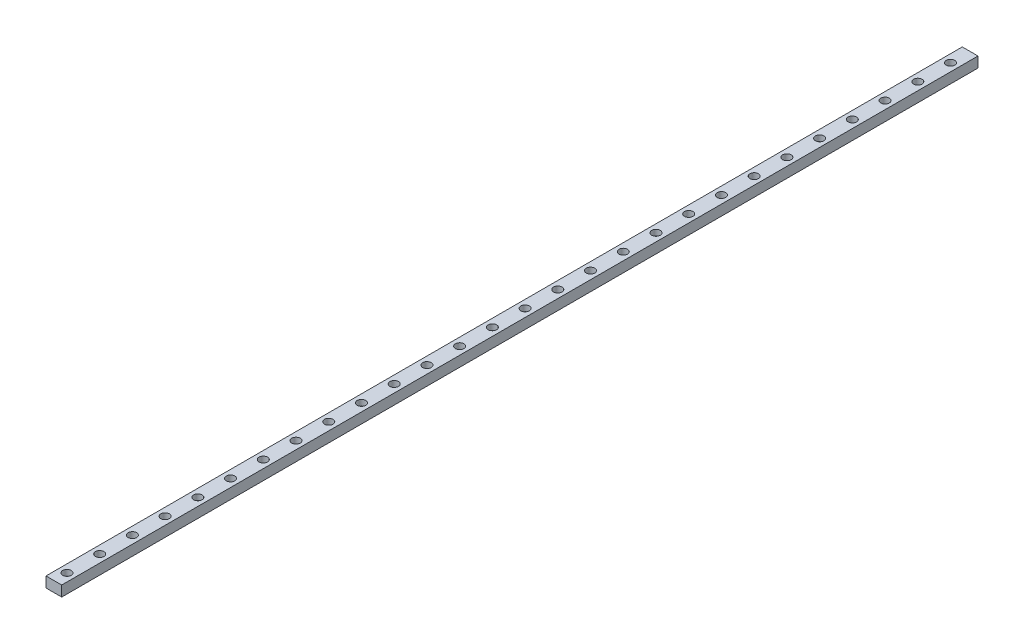
SolidWorks part; units mm, degrees
ref_plane "Front" through (0, 0, 0) normal (0, 0, 1) x (1, 0, 0)
ref_plane "Top" through (0, 0, 0) normal (0, 1, 0) x (1, 0, 0)
ref_plane "Right" through (0, 0, 0) normal (1, 0, 0) x (0, 0, -1)
sketch "Sketch1" plane through (0, 0, 0) normal (0, 0, 1) x (1, 0, 0)
  line L1 (0, 0) -> (12, 0)
  line L2 (0, 0) -> (0, 8)
  line L3 (0, 8) -> (12, 8)
  line L4 (12, 0) -> (12, 8)
  dimension "D1" = 12
  dimension "D2" = 8
extrude "Boss-Extrude1" add sketch "Sketch1" along normal blind 700
hole_wizard "CBORE for M3 SHCS1" positions "Sketch2" profile "Sketch3" counterbore size "M3" standard "ANSI Metric" end condition through all
sketch "Sketch2" plane through (0, 8, 0) normal (0, 1, 0) x (1, 0, 0)
  line L0 (12, -700) -> (0, -700) construction
  point P0 (6, -690)
  point P11 (6, -665)
  point P12 (6, -640)
  point P13 (6, -615)
  point P14 (6, -590)
  point P15 (6, -565)
  point P16 (6, -540)
  point P17 (6, -515)
  point P18 (6, -490)
  point P19 (6, -465)
  point P20 (6, -440)
  point P21 (6, -415)
  point P22 (6, -390)
  point P23 (6, -365)
  point P24 (6, -340)
  point P25 (6, -315)
  point P26 (6, -290)
  point P27 (6, -265)
  point P32 (6, -240)
  point P33 (6, -215)
  point P34 (6, -190)
  point P35 (6, -165)
  point P36 (6, -140)
  point P37 (6, -115)
  point P38 (6, -90)
  point P39 (6, -65)
  point P40 (6, -40)
  point P41 (6, -15)
  dimension "D1" = 10
  dimension "D2" = 28
sketch "Sketch3" plane through (6, 8, 690) normal (1, 0, 0) x (0, 0, 1)
  line L0 (0, 0) -> (0, 8)
  line L1 (0, 8) -> (1.7, 8)
  line L3 (1.7, 8) -> (1.7, 4.5)
  line L4 (1.7, 4.5) -> (3.25, 4.5)
  line L5 (3.25, 4.5) -> (3.25, 0)
  line L7 (3.25, 0) -> (0, 0)
  line L11 (0, -6.35) -> (0, 107.95) construction
  dimension "Thru Hole Dia." = 3.4
  dimension "Thru Hole Depth" = 8
  dimension "C'Bore Dia." = 6.5
  dimension "C'Bore Depth" = 4.5
equation "\"length\"=700"
equation "\"D1@Boss-Extrude1\"= \"length\""
